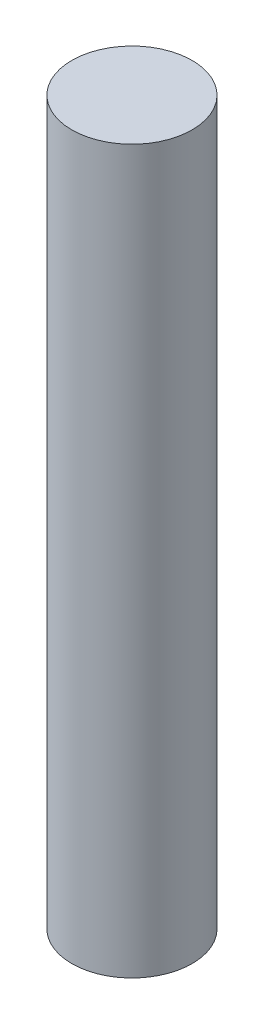
SolidWorks part; units mm, degrees
ref_plane "Front Plane" through (0, 0, 0) normal (0, 0, 1) x (1, 0, 0)
ref_plane "Top Plane" through (0, 0, 0) normal (0, 1, 0) x (1, 0, 0)
ref_plane "Right Plane" through (0, 0, 0) normal (1, 0, 0) x (0, 0, -1)
sketch "Sketch1" plane through (0, 0, 0) normal (0, 1, 0) x (1, 0, 0)
  circle A0 centre (0, 0) radius 1.25
  dimension "D1" = 2.5
extrude "Boss-Extrude1" add sketch "Sketch1" along normal blind 15
